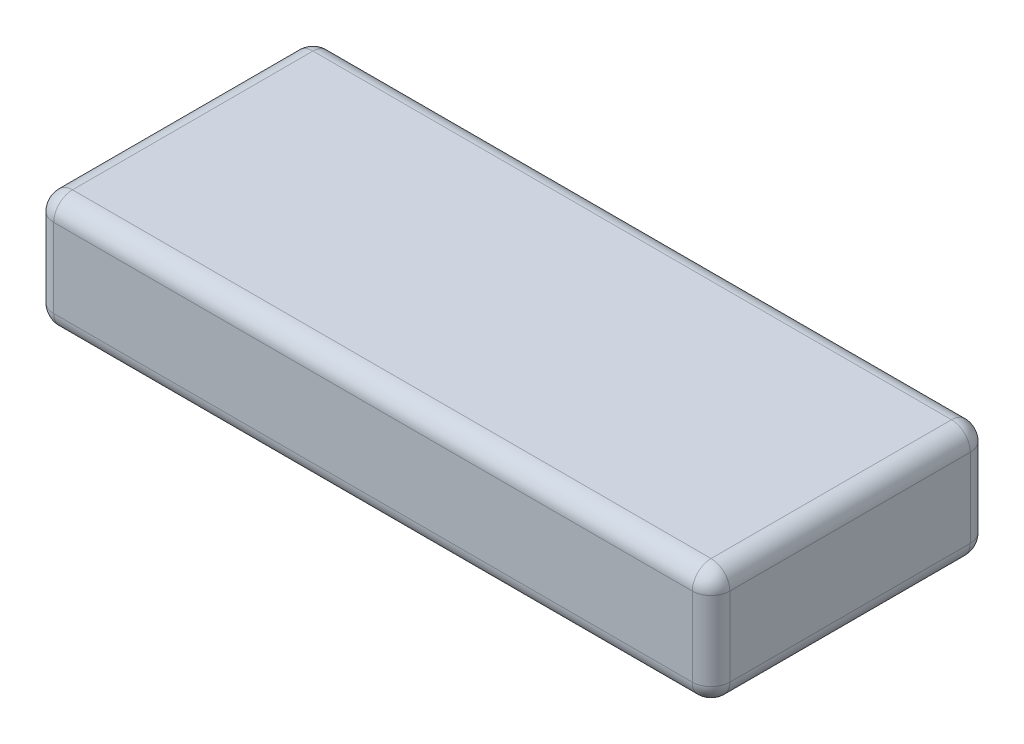
SolidWorks part; units mm, degrees
material "ABS"
ref_plane "Front Plane" through (0, 0, 0) normal (0, 0, 1) x (1, 0, 0)
ref_plane "Top Plane" through (0, 0, 0) normal (0, 1, 0) x (1, 0, 0)
ref_plane "Right Plane" through (0, 0, 0) normal (1, 0, 0) x (0, 0, -1)
sketch "Sketch1" plane through (0, 0, 0) normal (0, 1, 0) x (1, 0, 0)
  line L1 (-90, -37) -> (90, -37)
  line L2 (-90, -37) -> (-90, 37)
  line L3 (-90, 37) -> (90, 37)
  line L4 (90, -37) -> (90, 37)
  line L5 (-90, -37) -> (90, 37) construction
  line L6 (-90, 37) -> (90, -37) construction
  point P0 (0, 0)
  dimension "D1" = 180
  dimension "D2" = 74
extrude "Boss-Extrude1" add sketch "Sketch1" along normal blind 31
fillet "Fillet1" radius 5 12 edges at (0, 0, -37) (-90, 15.5, -37) (-90, 0, 0) (-90, 15.5, 37) (0, 0, 37) (90, 15.5, 37) (90, 15.5, -37) (90, 0, 0) (0, 31, 37) (-90, 31, 0) (0, 31, -37) (90, 31, 0)
